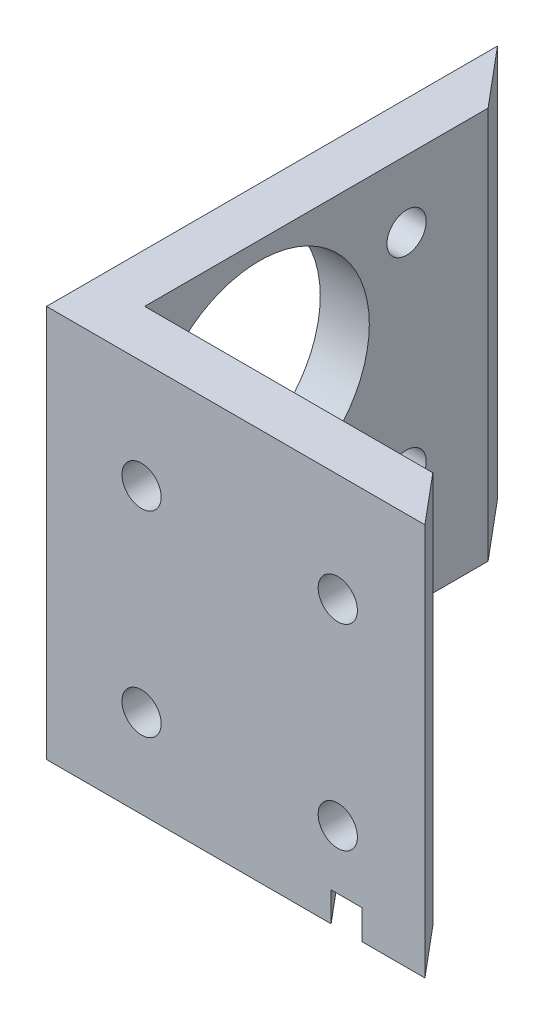
SolidWorks part; units mm, degrees
ref_plane "Front Plane" through (0, 0, 0) normal (0, 0, 1) x (1, 0, 0)
ref_plane "Top Plane" through (0, 0, 0) normal (0, 1, 0) x (1, 0, 0)
ref_plane "Right Plane" through (0, 0, 0) normal (1, 0, 0) x (0, 0, -1)
sketch "Sketch2" plane through (0, 0, 0) normal (0, 1, 0) x (1, 0, 0)
  line L0 (0, 58.3726) -> (0, 0)
  line L1 (0, 0) -> (48.9804, 0)
  line L2 (48.9804, 0) -> (43.6521, 6.35)
  line L3 (6.35, 50.805) -> (6.35, 6.35)
  line L4 (6.35, 6.35) -> (43.6521, 6.35)
  line L5 (6.35, 50.805) -> (0, 58.3726)
  line L6 (43.6521, 6.35) -> (6.35, 50.805) construction
  line L7 (48.9804, 0) -> (48.9804, -50000) construction
  dimension "D1" = 40
  dimension "D2" = 6.35
  dimension "D3" = 6.35
  dimension "D4" = 76.2
extrude "Boss-Extrude1" add sketch "Sketch2" along normal blind 50.8
sketch "Sketch4" plane through (0, 0, -6.35) normal (0, 0, -1) x (-1, 0, 0)
  line L0 (-37.7011, 24.13) -> (-43.6521, 24.13) construction
  line L1 (-37.7011, 36.83) -> (-12.3011, 36.83) construction
  line L2 (-37.7011, 36.83) -> (-37.7011, 11.43) construction
  line L3 (-37.7011, 11.43) -> (-12.3011, 11.43) construction
  line L4 (-12.3011, 36.83) -> (-12.3011, 11.43) construction
  line L5 (-43.6521, 0) -> (-6.35, 0) construction
  line L6 (-43.6521, 50.8) -> (-43.6521, 0) construction
  line L7 (-12.3011, 24.13) -> (-6.35, 24.13) construction
  line L8 (-6.35, 50.8) -> (-6.35, 0) construction
  circle A0 centre (-37.7011, 36.83) radius 2.54
  circle A1 centre (-12.3011, 36.83) radius 2.54
  circle A2 centre (-37.7011, 11.43) radius 2.54
  circle A3 centre (-12.3011, 11.43) radius 2.54
  dimension "D1" = 5.08
  dimension "D2" = 25.4
  dimension "D3" = 24.13
extrude "Cut-Extrude2" cut sketch "Sketch4" against normal up to next
sketch "Sketch3" plane through (6.35, 0, 0) normal (1, 0, 0) x (0, 0, -1)
  line L0 (6.985, 26.0871) -> (6.985, -49973.9129) construction
  line L1 (21.209, 48.4759) -> (50021.209, 48.4759) construction
  line L2 (28.9325, 34.2519) -> (50028.9325, 34.2519) construction
  line L3 (6.985, 15.2019) -> (13.335, 15.2019) construction
  line L4 (13.335, 15.2019) -> (40.259, 15.2019) construction
  line L5 (21.209, 27.8847) -> (21.209, 50027.8847) construction
  line L6 (6.35, 8.89) -> (6.35, 13.97) construction
  line L7 (6.35, 8.89) -> (6.35, 13.97) construction
  line L8 (40.259, 15.2019) -> (40.259, 42.1259) construction
  line L9 (6.35, 11.43) -> (50006.35, 11.43) construction
  line L10 (0, 50.8) -> (0, 0) construction
  line L11 (40.259, 42.1259) -> (40.259, 48.4759) construction
  circle A0 centre (13.335, 15.2019) radius 2.54
  circle A1 centre (21.209, 34.2519) radius 14.224
  circle A2 centre (40.259, 15.2019) radius 2.54
  circle A3 centre (40.259, 42.1259) radius 2.54
  point P22 (6.35, 11.43)
  dimension "D1" = 5.08
  dimension "D2" = 28.448
  dimension "D7" = 19.05
  dimension "D3" = 22.8219
  dimension "D4" = 6.35
  dimension "D5" = 19.05
  dimension "D6" = 21.209
extrude "Cut-Extrude1" cut sketch "Sketch3" against normal up to next
sketch "Sketch5" plane through (0, 0, 0) normal (0, -1, 0) x (1, 0, 0)
  line L0 (0, -48.6438) -> (40.817, 0)
  line L1 (0, -58.3726) -> (0, 0) construction
  line L2 (0, 0) -> (48.9804, 0) construction
  line L3 (40.817, 0) -> (36.8381, 0)
  line L4 (36.8381, 0) -> (0, -43.902)
  line L5 (0, -43.902) -> (0, -48.6438)
  line L6 (6.35, -50.805) -> (0, -58.3726) construction
  dimension "D1" = 3.048
  dimension "D2" = 63.5
extrude "Cut-Extrude3" cut sketch "Sketch5" against normal blind 3.81
